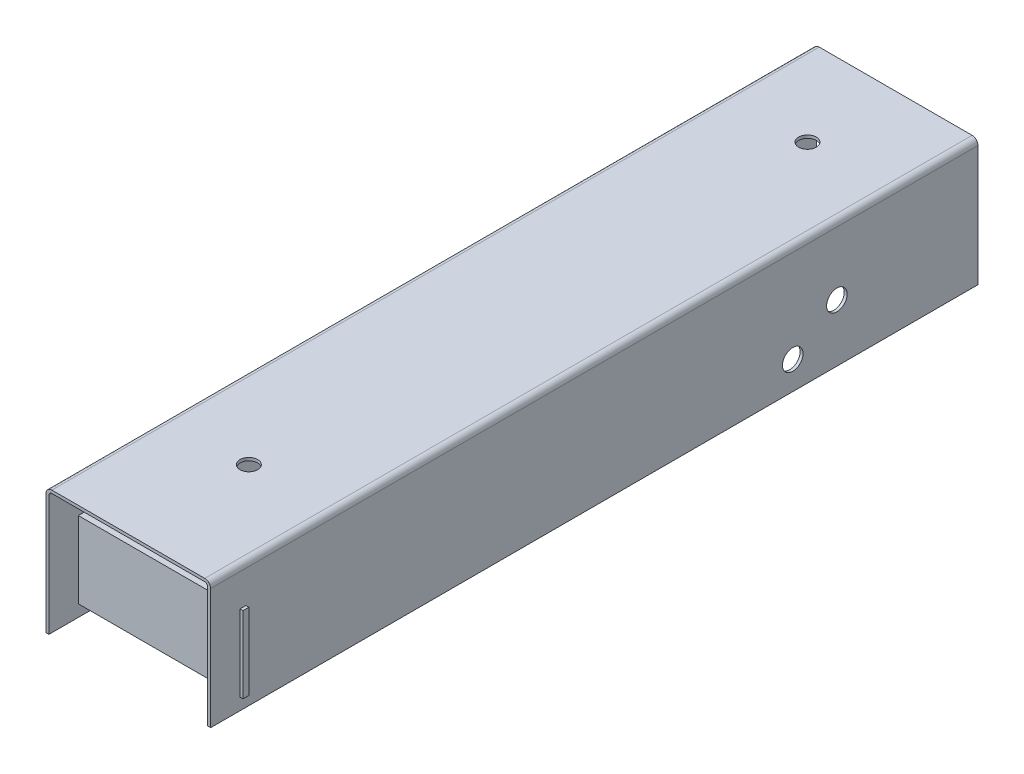
SolidWorks part; units mm, degrees
ref_plane "Płaszczyzna przednia" through (0, 0, 0) normal (0, 0, 1) x (1, 0, 0)
ref_plane "Płaszczyzna górna" through (0, 0, 0) normal (0, 1, 0) x (1, 0, 0)
ref_plane "Płaszczyzna prawa" through (0, 0, 0) normal (1, 0, 0) x (0, 0, -1)
sketch "Sketch1" plane through (0, 0, 0) normal (0, 0, 1) x (1, 0, 0)
  line L0 (26.6977, -20.5) -> (27, -20.5)
  line L1 (-28, 21.5) -> (28, 21.5)
  line L2 (-28, 21.5) -> (-28, -21.5)
  line L4 (28, 21.5) -> (28, -21.5)
  line L5 (-28, 21.5) -> (28, -21.5) construction
  line L6 (-28, -21.5) -> (28, 21.5) construction
  line L7 (-27, 20.5) -> (27, 20.5)
  line L8 (-27, 20.5) -> (-27, -20.5)
  line L9 (-27, -20.5) -> (-26.6977, -20.5)
  line L10 (27, 20.5) -> (27, -20.5)
  line L11 (-27, 20.5) -> (27, -20.5) construction
  line L12 (-27, -20.5) -> (27, 20.5) construction
  line L13 (-28, -21.5) -> (-27, -21.5)
  line L14 (-27, -21.5) -> (-27, -20.5)
  line L15 (28, -21.5) -> (27, -21.5)
  line L16 (27, -21.5) -> (27, -20.5)
  point P0 (0, 0)
  point P6 (0, 0)
  dimension "D1" = 56
  dimension "D2" = 43
  dimension "D3" = 54
  dimension "D4" = 41
extrude "Boss-Extrude1" add sketch "Sketch1" along normal blind 261 contours L16 L15 L4 L1 L2 L13 L14 L8 L7 L10
fillet "Fillet1" radius 2 2 edges at (-28, 21.5, 130.5) (28, 21.5, 130.5)
fillet "Fillet2" radius 1 2 edges at (27, 20.5, 130.5) (-27, 20.5, 130.5)
sketch "Sketch2" plane through (-27, 0, 0) normal (1, 0, 0) x (0, 0, -1)
  line L0 (-251, -21.5) -> (-251, 19.5) construction
  line L1 (-261, -21.5) -> (0, -21.5) construction
  line L2 (0, 19.5) -> (-261, 19.5) construction
  line L3 (-261, 19.5) -> (-261, -21.5) construction
  line L4 (-251, -17.5) -> (-261, -17.5) construction
  line L10 (-251, -17.5) -> (-249, -17.5)
  line L11 (-251, -17.5) -> (-251, 8.5)
  line L12 (-251, 8.5) -> (-249, 8.5)
  line L13 (-249, -17.5) -> (-249, 8.5)
  line L14 (-251, -17.5) -> (-249, 8.5) construction
  line L15 (-251, 8.5) -> (-249, -17.5) construction
  point P14 (-250, -4.5)
  dimension "D1" = 10
  dimension "D2" = 4
  dimension "D3" = 2
  dimension "D4" = 26
extrude "Boss-Extrude2" add sketch "Sketch2" along normal blind 56 and the other way blind 2
sketch "Sketch3" plane through (0, 21.5, 0) normal (0, 1, 0) x (1, 0, 0)
  line L0 (0, 0) -> (0, -261) construction
  line L1 (-26, 0) -> (26, 0) construction
  line L2 (-26, -261) -> (26, -261) construction
  circle A0 centre (0, -30) radius 3
  circle A1 centre (0, -220) radius 3
  dimension "D1" = 30
  dimension "D2" = 41
extrude "Cut-Extrude1" cut sketch "Sketch3" against normal blind 11
sketch "Sketch4" plane through (-28, 0, 0) normal (-1, 0, 0) x (0, 0, 1)
  line L0 (0, 21.5) -> (261, 21.5) construction
  line L1 (206, 16.5) -> (236, 16.5)
  line L2 (206, 16.5) -> (206, -23.5)
  line L3 (206, -23.5) -> (236, -23.5)
  line L4 (236, 16.5) -> (236, -23.5)
  line L5 (206, 16.5) -> (236, -23.5) construction
  line L6 (206, -23.5) -> (236, 16.5) construction
  line L7 (261, 19.5) -> (261, -21.5) construction
  point P4 (221, -3.5)
  dimension "D1" = 5
  dimension "D2" = 25
  dimension "D3" = 30
  dimension "D4" = 40
extrude "Cut-Extrude2" cut sketch "Sketch4" against normal blind 10
sketch "Sketch5" plane through (-28, 0, 0) normal (-1, 0, 0) x (0, 0, 1)
  line L0 (48, -21.5) -> (48, 21.5) construction
  line L1 (206, -21.5) -> (0, -21.5) construction
  line L2 (0, 21.5) -> (261, 21.5) construction
  line L3 (261, 19.5) -> (261, -21.5) construction
  line L4 (48, -2) -> (63, -2) construction
  line L5 (63, -2) -> (63, -12) construction
  circle A0 centre (48, -2) radius 3.5
  circle A1 centre (63, -12) radius 3.5
  dimension "D1" = 213
  dimension "D2" = 23.5
extrude "Cut-Extrude3" cut sketch "Sketch5" against normal blind 69
